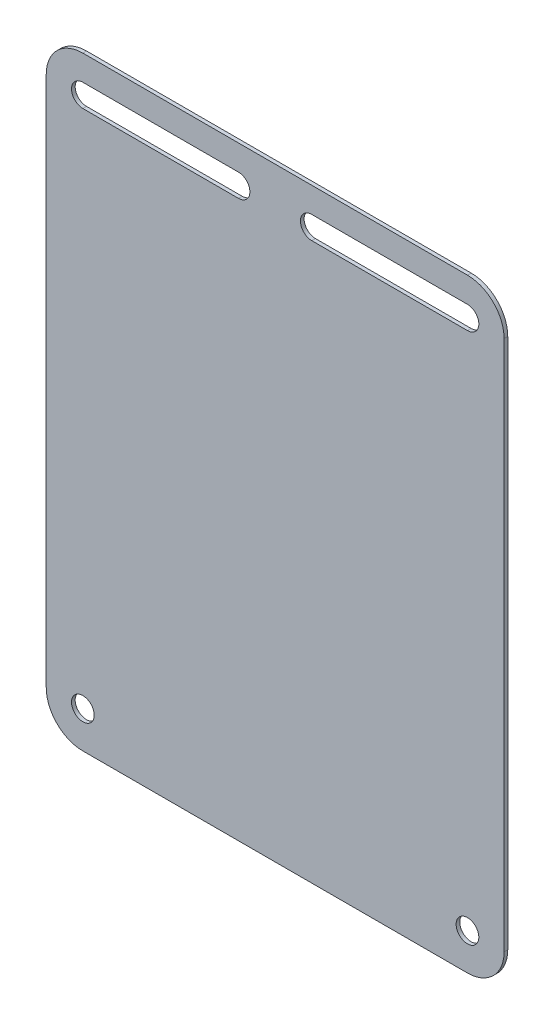
SolidWorks part; units mm, degrees
ref_plane "前视基准面" through (0, 0, 0) normal (0, 0, 1) x (1, 0, 0)
ref_plane "上视基准面" through (0, 0, 0) normal (0, 1, 0) x (1, 0, 0)
ref_plane "右视基准面" through (0, 0, 0) normal (1, 0, 0) x (0, 0, -1)
sketch "草图1" plane through (0, 0, 0) normal (0, 0, 1) x (1, 0, 0)
  line L0 (-67.6098, -55.5761) -> (158.563, -55.5761) construction
  line L1 (-7.4565, 26.9239) -> (117.5435, 26.9239)
  line L2 (-7.4565, 26.9239) -> (-7.4565, -138.0761)
  line L3 (-7.4565, -138.0761) -> (117.5435, -138.0761)
  line L4 (117.5435, 26.9239) -> (117.5435, -138.0761)
  line L5 (55.0435, 22.4605) -> (55.0435, -148.7997) construction
  line L6 (107.5435, 20.0239) -> (65.0435, 20.0239)
  line L7 (107.5435, 13.8239) -> (65.0435, 13.8239)
  line L8 (45.0435, 20.0239) -> (2.5435, 20.0239)
  line L9 (45.0435, 13.8239) -> (2.5435, 13.8239)
  arc A0 (2.5435, 20.0239) -> (2.5435, 13.8239) centre (2.5435, 16.9239) ccw
  arc A1 (107.5435, 20.0239) -> (107.5435, 13.8239) centre (107.5435, 16.9239) cw
  circle A2 centre (107.5435, -128.0761) radius 3.1
  circle A3 centre (2.5435, -128.0761) radius 3.1
  arc A4 (65.0435, 20.0239) -> (65.0435, 13.8239) centre (65.0435, 16.9239) ccw
  arc A5 (45.0435, 20.0239) -> (45.0435, 13.8239) centre (45.0435, 16.9239) cw
  dimension "D3" = 10
  dimension "D4" = 6.2
  dimension "D6" = 10
  dimension "D1" = 165
  dimension "D2" = 125
  dimension "D5" = 10
extrude "凸台-拉伸1" add sketch "草图1" along normal blind 1
fillet "圆角1" radius 10 4 edges at (117.5435, -138.0761, 0.5) (-7.4565, -138.0761, 0.5) (-7.4565, 26.9239, 0.5) (117.5435, 26.9239, 0.5)
